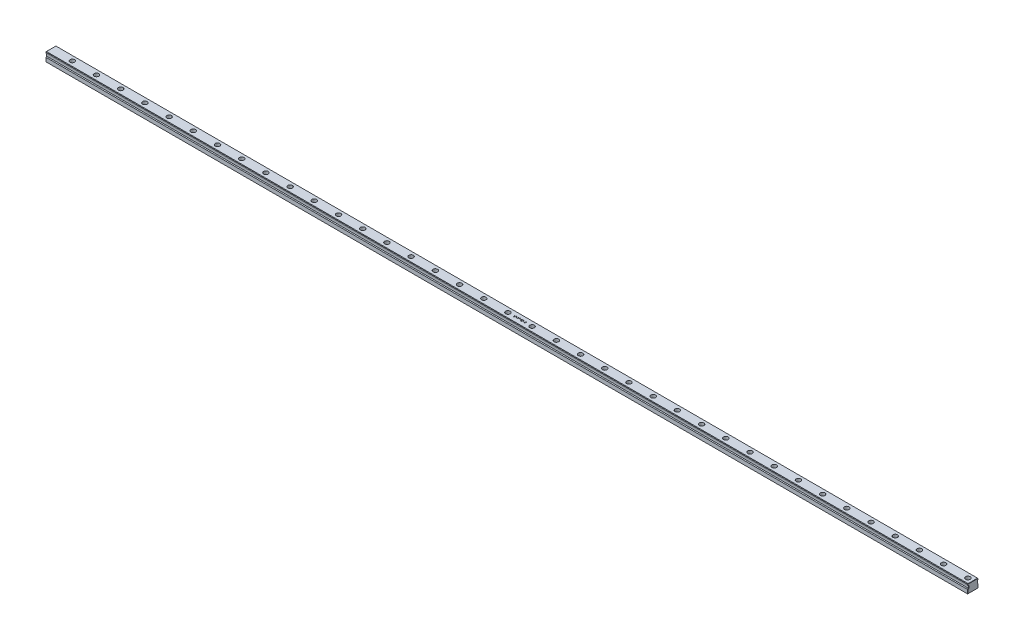
SolidWorks part; units mm, degrees
ref_plane "Front Plane" through (0, 0, 0) normal (0, 0, 1) x (1, 0, 0)
ref_plane "Top Plane" through (0, 0, 0) normal (0, 1, 0) x (1, 0, 0)
ref_plane "Right Plane" through (0, 0, 0) normal (1, 0, 0) x (0, 0, -1)
sketch "Sketch1" plane through (0, 0, 0) normal (1, 0, 0) x (0, 0, -1)
  line L0 (-22.5, 0) -> (22.5, 0)
  line L1 (0, 0) -> (0, 55.3871) construction
  line L2 (-20.5, 38) -> (20.5, 38)
  line L3 (22.5, 17) -> (22.5, 0)
  line L4 (-20.5, 38) -> (-22.5, 36)
  line L5 (-22.5, 36) -> (-22.5, 32)
  line L6 (-22.5, 32) -> (-19.5, 29)
  line L7 (-19.5, 29) -> (-19.5, 20)
  line L8 (-19.5, 20) -> (-22.5, 17)
  line L9 (-22.5, 17) -> (-22.5, 0)
  line L10 (19.5, 20) -> (22.5, 17)
  line L11 (19.5, 29) -> (19.5, 20)
  line L12 (22.5, 32) -> (19.5, 29)
  line L13 (22.5, 36) -> (22.5, 32)
  line L14 (20.5, 38) -> (22.5, 36)
  point P18 (0, 38)
  dimension "D3" = 3
  dimension "D4" = 2
  dimension "D5" = 2
  dimension "D6" = 4
  dimension "D7" = 3
  dimension "D8" = 9
extrude "Boss-Extrude1" add sketch "Sketch1" along normal blind 4000
sketch "Sketch2" plane through (0, 38, 0) normal (0, 1, 0) x (1, 0, 0)
  line L0 (4000, 20.5) -> (4000, -20.5) construction
  circle A0 centre (3977.5, 0) radius 10
  dimension "D2" = 20
  dimension "D1" = 22.5
extrude "Cut-Extrude1" cut sketch "Sketch2" against normal blind 17
sketch "Sketch3" plane through (0, 21, 0) normal (0, 1, 0) x (1, 0, 0)
  circle A0 centre (3977.5, 0) radius 7
  dimension "D1" = 14
extrude "Cut-Extrude2" cut sketch "Sketch3" against normal through all
pattern_linear "LPattern1" count 38 spacing 105 along (-1, 0, 0) of "Cut-Extrude1", "Cut-Extrude2"
chamfer "Chamfer1" distance 1 angle 45 28 edges at (0, 0, 0) (0, 8.5, -22.5) (0, 18.5, -21) (0, 24.5, -19.5) (0, 30.5, -21) (0, 34, -22.5) (0, 37, -21.5) (0, 38, 0) (0, 37, 21.5) (0, 34, 22.5) (0, 30.5, 21) (0, 24.5, 19.5) (0, 18.5, 21) (0, 8.5, 22.5) (4000, 18.5, 21) (4000, 24.5, 19.5) (4000, 30.5, 21) (4000, 34, 22.5) (4000, 37, 21.5) (4000, 38, 0) (4000, 37, -21.5) (4000, 34, -22.5) (4000, 30.5, -21) (4000, 24.5, -19.5) (4000, 18.5, -21) (4000, 8.5, -22.5) (4000, 0, 0) (4000, 8.5, 22.5)
sketch "Sketch5" plane through (0, 38, 0) normal (0, 1, 0) x (1, 0, 0)
  text T0 "SHN 45 B" font "Century Gothic" height in points 35
extrude "Cut-Extrude3" cut sketch "Sketch5" against normal blind 2
